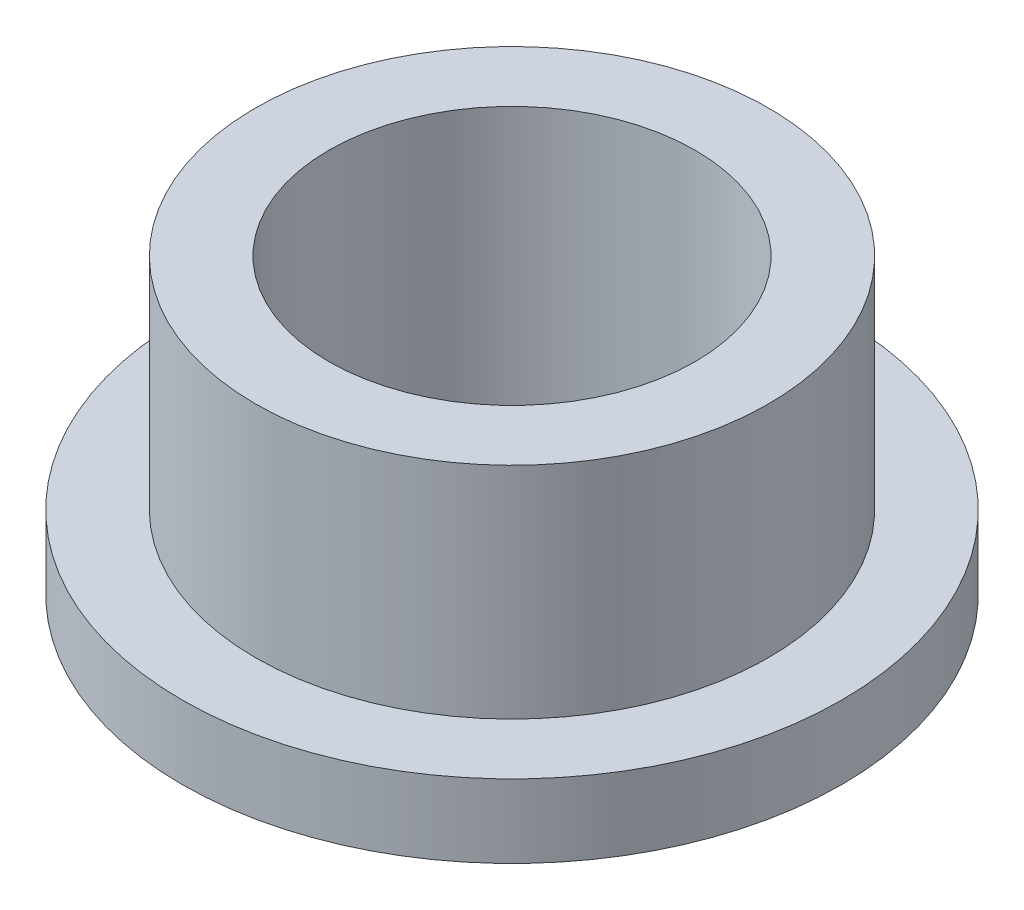
SolidWorks part; units mm, degrees
ref_plane "Front" through (0, 0, 0) normal (0, 0, 1) x (1, 0, 0)
ref_plane "Top" through (0, 0, 0) normal (0, 1, 0) x (1, 0, 0)
ref_plane "Right" through (0, 0, 0) normal (1, 0, 0) x (0, 0, -1)
sketch "Sketch1" plane through (0, 0, 0) normal (0, 1, 0) x (1, 0, 0)
  circle A0 centre (0, 0) radius 5
  circle A1 centre (0, 0) radius 9
  dimension "D1" = 10
  dimension "D2" = 18
extrude "Boss-Extrude1" add sketch "Sketch1" along normal blind 2
sketch "Sketch2" plane through (0, 2, 0) normal (0, 1, 0) x (1, 0, 0)
  circle A0 centre (0, 0) radius 5
  circle A1 centre (0, 0) radius 7
  dimension "D1" = 14
  dimension "D2" = 10
extrude "Boss-Extrude2" add sketch "Sketch2" along normal blind 6
